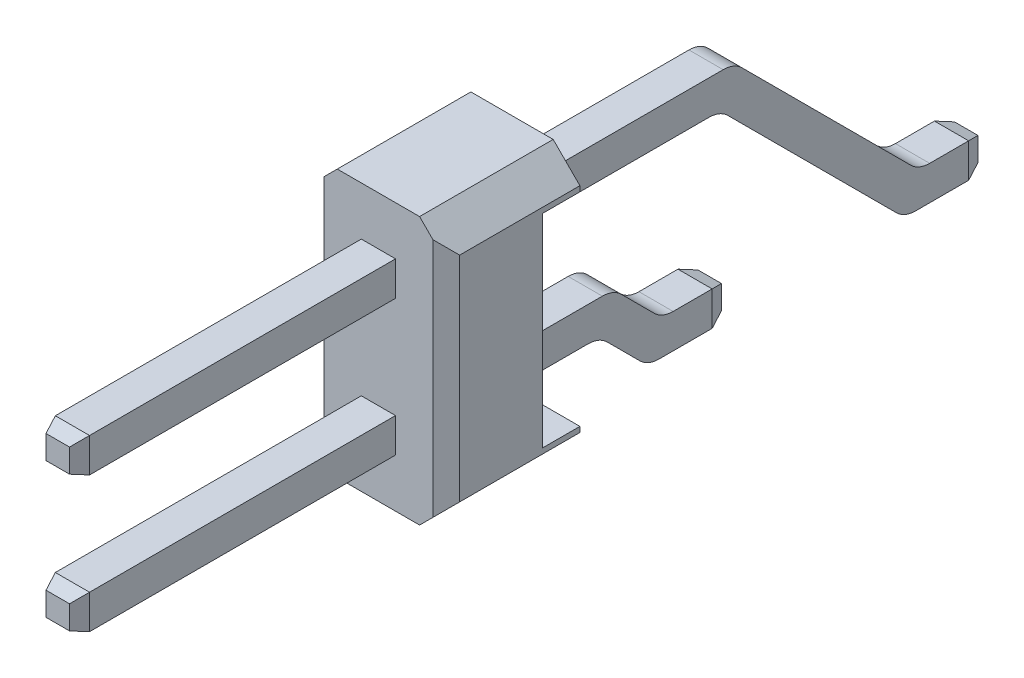
SolidWorks part; units mm, degrees
ref_plane "Спереди" through (0, 0, 0) normal (0, 0, 1) x (1, 0, 0)
ref_plane "Сверху" through (0, 0, 0) normal (0, 1, 0) x (1, 0, 0)
ref_plane "Справа" through (0, 0, 0) normal (1, 0, 0) x (0, 0, -1)
sketch "Эскиз1" plane through (0, 0, 0) normal (1, 0, 0) x (0, 0, -1)
  line L0 (-0.7385, 0) -> (0.7385, 0)
  line L1 (4.0615, 0) -> (5.5385, 0)
  line L2 (5.5385, 0) -> (5.5385, 0.64)
  line L3 (0.7385, 0) -> (0.7385, 0.64)
  line L4 (-0.7385, 0) -> (-1.6485, 0.91)
  line L5 (4.0615, 0) -> (0.6115, 3.45)
  line L6 (-1.6485, 0.91) -> (-11.4615, 0.91)
  line L7 (0.7385, 0.64) -> (-0.4734, 0.64)
  line L10 (-1.3834, 1.55) -> (-0.4734, 0.64)
  line L11 (-1.3834, 1.55) -> (-11.4615, 1.55)
  line L12 (-11.4615, 1.55) -> (-11.4615, 0.91)
  line L13 (5.5385, 0.64) -> (4.3266, 0.64)
  line L14 (4.3266, 0.64) -> (0.8766, 4.09)
  line L15 (0.8766, 4.09) -> (-11.4615, 4.09)
  line L16 (-11.4615, 4.09) -> (-11.4615, 3.45)
  line L17 (-11.4615, 3.45) -> (0.6115, 3.45)
  point P4 (0, 0)
  point P12 (-11.4615, 1.23)
  point P13 (0.7385, 0.32)
  point P19 (-11.4615, 3.77)
  dimension "D1" = 1.477
  dimension "D2" = 1.477
  dimension "D3" = 4.8
  dimension "D4" = 0.64
  dimension "D5" = 0.64
  dimension "D6" = 12.2
  dimension "D7" = 1.23
  dimension "D8" = 0.64
  dimension "D9" = 45
  dimension "D10" = 135
  dimension "D11" = 0.64
  dimension "D12" = 0.64
  dimension "D13" = 2.54
  dimension "D14" = 135
  dimension "D15" = 0.64
extrude "Бобышка-Вытянуть1" add sketch "Эскиз1" against normal mid plane 0.64
chamfer "Фаска1" distance 0.1 angle 70 8 edges at (-0.32, 0.32, -5.5385) (0, 0, -5.5385) (0, 0.64, -5.5385) (0.32, 0.32, -5.5385) (0, 3.45, 11.4615) (-0.32, 3.77, 11.4615) (0, 4.09, 11.4615) (0.32, 3.77, 11.4615)
fillet "Скругление1" radius 0.5 4 edges at (0, 0.64, -4.3266) (0, 0, -4.0615) (0, 3.45, -0.6115) (0, 4.09, -0.8766)
chamfer "Фаска2" distance 0.1 angle 70 8 edges at (0, 0.64, -0.7385) (-0.32, 0.32, -0.7385) (0, 0, -0.7385) (0.32, 0.32, -0.7385) (0, 0.91, 11.4615) (-0.32, 1.23, 11.4615) (0, 1.55, 11.4615) (0.32, 1.23, 11.4615)
fillet "Скругление2" radius 0.5 4 edges at (0, 0, 0.7385) (0, 0.91, 1.6485) (0, 0.64, 0.4734) (0, 1.55, 1.3834)
ref_plane "Плоскость1" through (0, 0, 3.661) normal (0, 0, 1) x (1, 0, 0)
sketch "Эскиз2" plane through (0, 0, 3.661) normal (0, 0, 1) x (1, 0, 0)
  line L0 (0, -1000) -> (0, 49000) construction
  line L1 (-1.27, 5) -> (1.27, 5)
  line L2 (-1.27, 5) -> (-1.27, 0)
  line L3 (-1.27, 0) -> (1.27, 0)
  line L4 (1.27, 5) -> (1.27, 0)
  line L5 (-1.27, 5) -> (1.27, 0) construction
  line L6 (-1.27, 0) -> (1.27, 5) construction
  point P0 (0, 2.5)
  point P6 (0, 0)
  dimension "D1" = 5
  dimension "D2" = 2.54
  dimension "D3" = 2.5
extrude "Бобышка-Вытянуть2" add sketch "Эскиз2" along normal blind 1.8
chamfer "Фаска3" distance 0.5 4 edges at (-1.27, 0, 4.561) (1.27, 0, 4.561) (-1.27, 5, 4.561) (1.27, 5, 4.561)
chamfer "Фаска4" distance 0.25 angle 57.296 2 edges at (-1.27, 2.5, 5.461) (1.27, 2.5, 5.461)
sketch "Эскиз3" plane through (0, 0, 3.661) normal (0, 0, -1) x (-1, 0, 0)
  line L0 (-1.27, 4.5) -> (-0.77, 5)
  line L1 (-0.77, 5) -> (0.77, 5)
  line L2 (0.77, 5) -> (1.27, 4.5)
  line L3 (1.27, 4.5) -> (1.27, 0.5) construction
  line L4 (1.27, 4.5) -> (0.77, 5) construction
  line L5 (1.27, 4.5) -> (1.27, 4.4)
  line L6 (1.27, 4.4) -> (-1.27, 4.4)
  line L7 (-1.27, 0.5) -> (-1.27, 4.5) construction
  line L8 (-1.27, 4.4) -> (-1.27, 4.5)
  line L9 (-1001.27, 2.5) -> (48998.73, 2.5) construction
  line L10 (-1.27, 0.6) -> (-1.27, 0.5)
  line L11 (1.27, 0.6) -> (-1.27, 0.6)
  line L12 (1.27, 0.5) -> (1.27, 0.6)
  line L13 (0.77, 0) -> (1.27, 0.5)
  line L14 (-0.77, 0) -> (0.77, 0)
  line L15 (-1.27, 0.5) -> (-0.77, 0)
  point P12 (0, 5)
  point P19 (-1.27, 2.5)
  dimension "D1" = 0.6
extrude "Бобышка-Вытянуть3" add sketch "Эскиз3" along normal blind 0.7
